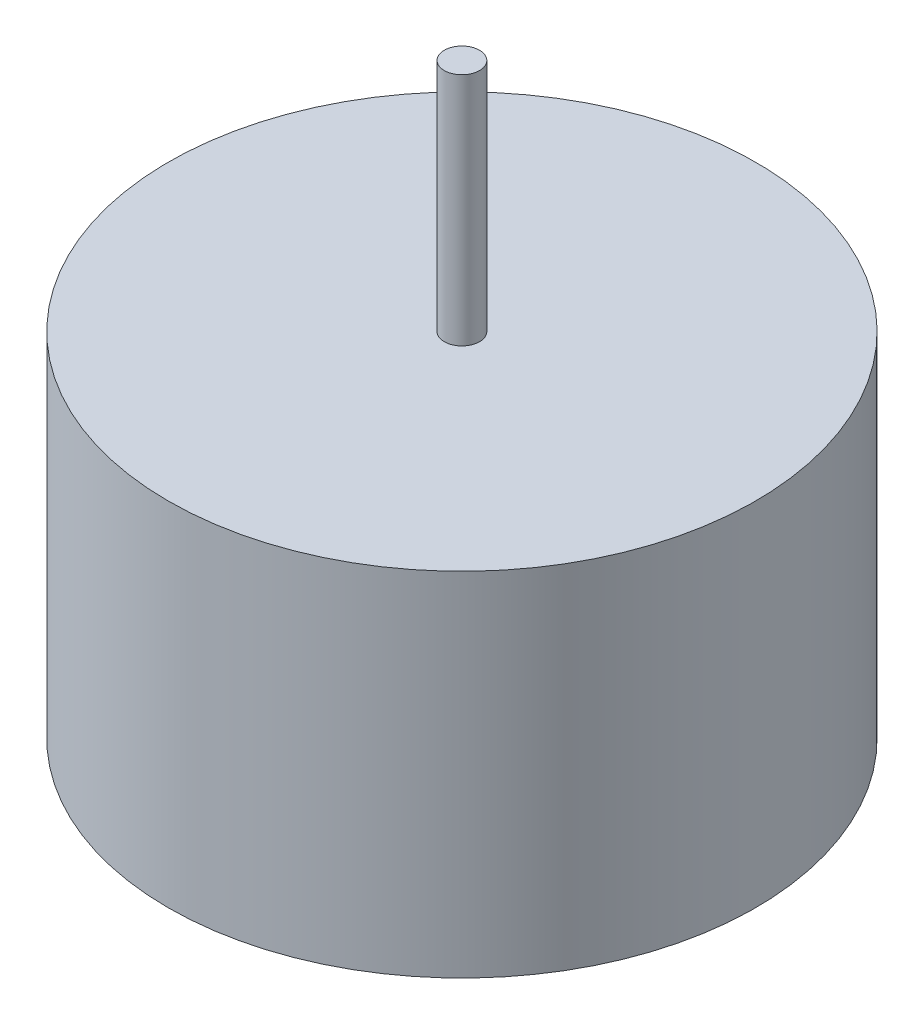
SolidWorks part; units mm, degrees
ref_plane "Front Plane" through (0, 0, 0) normal (0, 0, 1) x (1, 0, 0)
ref_plane "Top Plane" through (0, 0, 0) normal (0, 1, 0) x (1, 0, 0)
ref_plane "Right Plane" through (0, 0, 0) normal (1, 0, 0) x (0, 0, -1)
sketch "Sketch1" plane through (0, 0, 0) normal (0, 1, 0) x (1, 0, 0)
  circle A0 centre (0, 0) radius 25
extrude "Boss-Extrude1" add sketch "Sketch1" along normal blind 30
sketch "Sketch2" plane through (0, 30, 0) normal (0, 1, 0) x (1, 0, 0)
  circle A0 centre (0, 0) radius 1.5
extrude "Boss-Extrude2" add sketch "Sketch2" along normal blind 20
